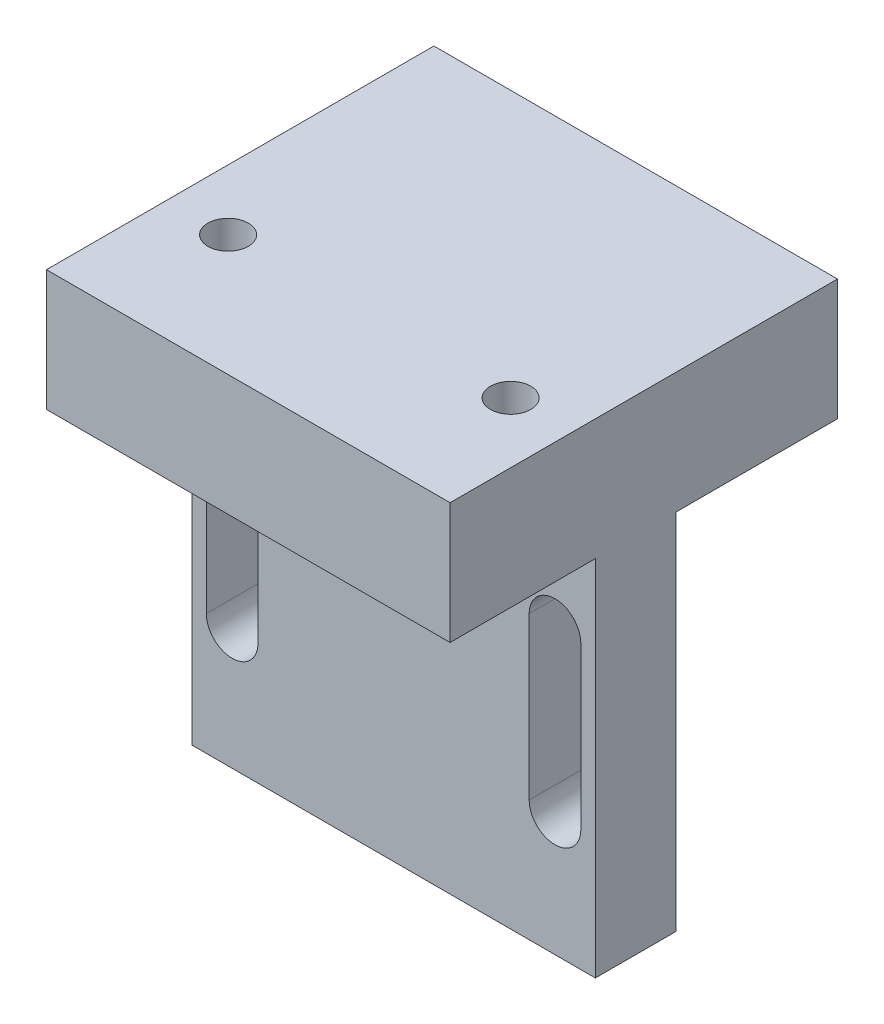
SolidWorks part; units mm, degrees
ref_plane "前视基准面" through (0, 0, 0) normal (0, 0, 1) x (1, 0, 0)
ref_plane "上视基准面" through (0, 0, 0) normal (0, 1, 0) x (1, 0, 0)
ref_plane "右视基准面" through (0, 0, 0) normal (1, 0, 0) x (0, 0, -1)
sketch "草图1" plane through (0, 0, 0) normal (0, 0, 1) x (1, 0, 0)
  line L1 (25, -30) -> (-25, -30)
  line L2 (25, -30) -> (25, 30)
  line L3 (25, 30) -> (-25, 30)
  line L4 (-25, -30) -> (-25, 30)
  line L5 (25, -30) -> (-25, 30) construction
  line L6 (25, 30) -> (-25, -30) construction
  point P0 (0, 0)
  dimension "D1" = 50
  dimension "D2" = 60
extrude "凸台-拉伸1" add sketch "草图1" along normal blind 30
sketch "草图2" plane through (0, 0, 0) normal (0, 0, -1) x (-1, 0, 0)
  line L0 (25, 30) -> (25, -30) construction
  line L1 (-25, -30) -> (25, -30)
  line L2 (-25, -30) -> (-25, 15)
  line L3 (-25, 15) -> (25, 15)
  line L4 (25, -30) -> (25, 15)
  line L5 (-25, 30) -> (25, 30) construction
  dimension "D1" = 15
extrude "切除-拉伸1" cut sketch "草图2" against normal offset from surface (20 mm away) 10 up to face at (0, 0, 30)
sketch "草图3" plane through (0, 0, 20) normal (0, 0, -1) x (-1, 0, 0)
  line L0 (0, -30) -> (0, -5) construction
  line L1 (-25, -30) -> (25, -30) construction
  line L2 (0, -5) -> (-20, -5) construction
  line L3 (-20, -15) -> (-20, 5) construction
  line L4 (-23.2, -15) -> (-23.2, 5)
  line L5 (-16.8, -15) -> (-16.8, 5)
  line L6 (20, -15) -> (20, 5) construction
  line L7 (23.2, -15) -> (23.2, 5)
  line L8 (16.8, -15) -> (16.8, 5)
  arc A0 (-23.2, -15) -> (-16.8, -15) centre (-20, -15) ccw
  arc A1 (-16.8, 5) -> (-23.2, 5) centre (-20, 5) ccw
  arc A2 (23.2, -15) -> (16.8, -15) centre (20, -15) cw
  arc A3 (16.8, 5) -> (23.2, 5) centre (20, 5) cw
  point P8 (-20, -5)
  point P15 (20, -5)
  dimension "D2" = 3.2
  dimension "D1" = 20
  dimension "D3" = 40
  dimension "D4" = 25
extrude "切除-拉伸2" cut sketch "草图3" against normal through all
sketch "草图6" plane through (0, 0, 30) normal (0, 0, 1) x (1, 0, 0)
  line L4 (25, 15) -> (25, 30)
  line L5 (-25, 15) -> (25, 15)
  line L6 (-25, 30) -> (-25, 15)
  line L7 (25, 30) -> (-25, 30)
  line L8 (25, 15) -> (25, 30)
  line L9 (-25, 15) -> (25, 15)
  line L10 (-25, 30) -> (-25, 15)
  line L11 (25, 30) -> (-25, 30)
  dimension "D1" = 0
extrude "凸台-拉伸2" add sketch "草图6" along normal blind 18
sketch "草图4" plane through (0, 30, 0) normal (0, 1, 0) x (1, 0, 0)
  line L0 (0, 0) -> (0, -33) construction
  line L1 (25, 0) -> (-25, 0) construction
  line L2 (0, -33) -> (17.5, -33) construction
  line L3 (25, -48) -> (-25, -48) construction
  circle A0 centre (17.5, -33) radius 5.3229
  circle A1 centre (-17.5, -33) radius 5.3229
  dimension "D1" = 35
  dimension "D2" = 15
hole_wizard "M6 螺纹孔1" positions "3D草图1" profile "草图5" tap size "M6" standard "Iso"
sketch3d "3D草图1"
  point P0 (17.5, 30, 33)
  point P3 (-17.5, 30, 33)
sketch "草图5" plane through (17.5, 30, 33) normal (1, 0, 0) x (0, 0, 1)
  line L0 (0, 0) -> (0, 16.5022)
  line L1 (0, 16.5022) -> (2.5, 15)
  line L2 (2.5, 15) -> (2.5, 0)
  line L5 (2.5, 0) -> (0, 0)
  line L10 (0, 16.5022) -> (-2.5, 15) construction
  line L11 (0, -6.35) -> (0, 107.95) construction
  dimension "螺纹孔钻头直径" = 5
  dimension "螺纹孔钻头深度" = 15
  dimension "导头角度" = 118
